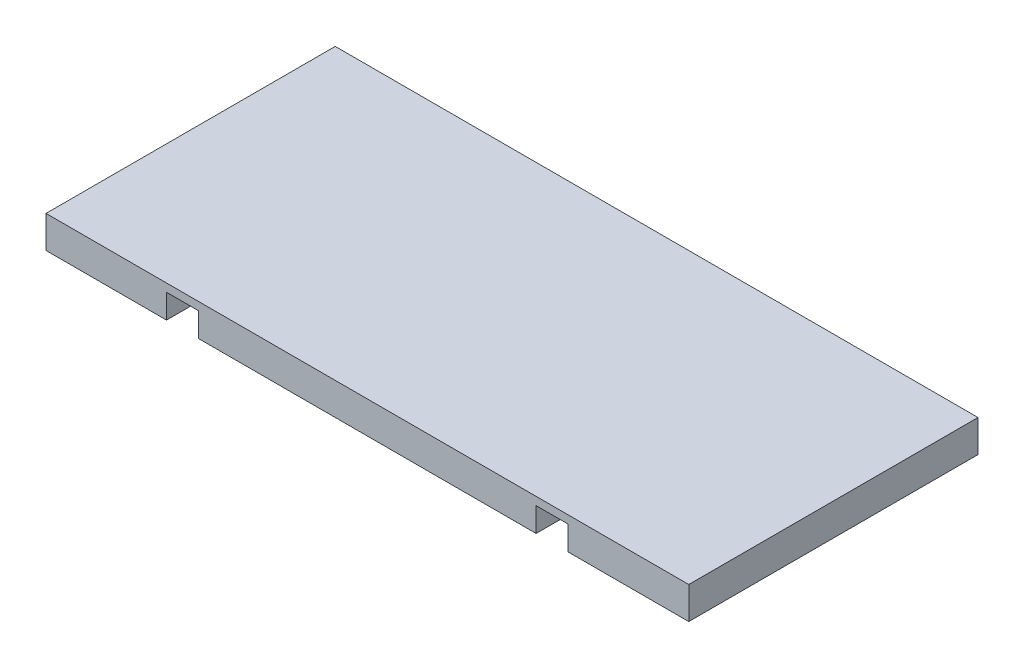
SolidWorks part; units mm, degrees
ref_plane "Front Plane" through (0, 0, 0) normal (0, 0, 1) x (1, 0, 0)
ref_plane "Top Plane" through (0, 0, 0) normal (0, 1, 0) x (1, 0, 0)
ref_plane "Right Plane" through (0, 0, 0) normal (1, 0, 0) x (0, 0, -1)
sketch "Sketch1" plane through (0, 0, 0) normal (0, 0, 1) x (1, 0, 0)
  line L1 (-20, -2) -> (-12.5, -2)
  line L2 (-20, -2) -> (-20, 0)
  line L4 (20, -2) -> (20, 0)
  line L10 (0, 0) -> (0, -2) construction
  line L11 (-20, 0) -> (20, 0)
  line L18 (-10.5, -2) -> (10.5, -2)
  line L20 (-12.5, -2) -> (-12.5, -0.5)
  line L21 (-12.5, -0.5) -> (-10.5, -0.5)
  line L22 (-10.5, -2) -> (-10.5, -0.5)
  line L23 (10.5, -2) -> (10.5, -0.5)
  line L24 (12.5, -2) -> (12.5, -0.5)
  line L25 (12.5, -0.5) -> (10.5, -0.5)
  line L26 (12.5, -2) -> (20, -2)
  point P4 (0, 0)
  point P7 (0, 0)
  point P11 (0, 0)
  point P12 (18.9791, 2.7307)
  point P13 (0, -1.0256)
  point P14 (0, 0)
  dimension "D1" = 2
  dimension "D2" = 10.5
  dimension "D3" = 2
  dimension "D4" = 40
  dimension "D5" = 1.5
extrude "Boss-Extrude1" add sketch "Sketch1" along normal blind 18
